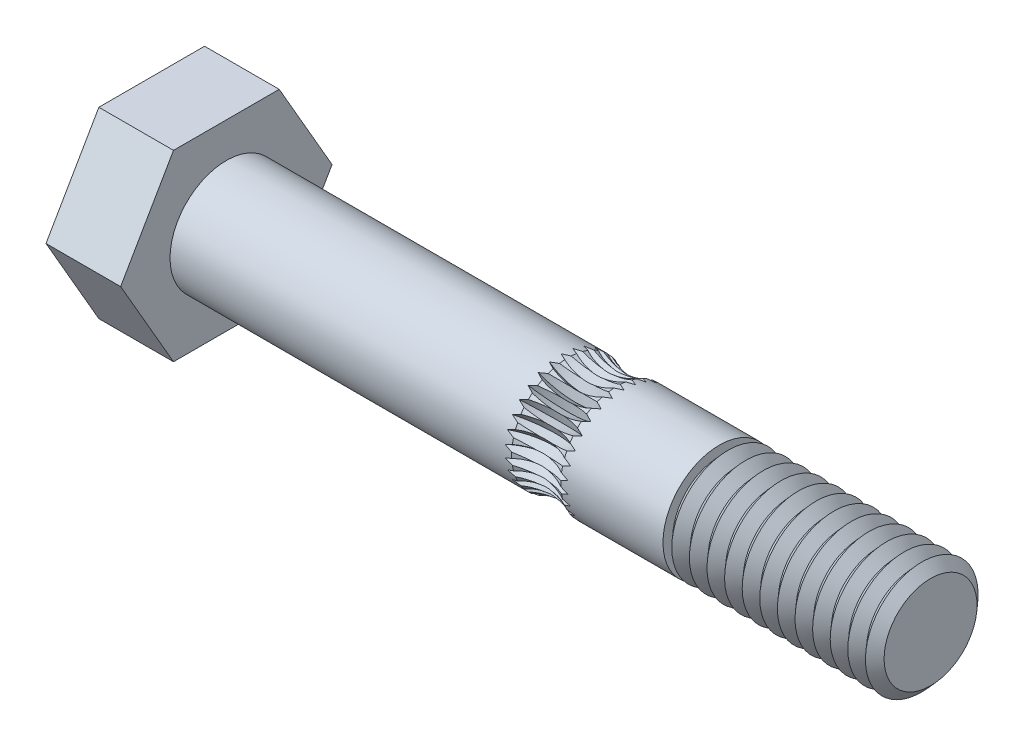
SolidWorks part; units mm, degrees
ref_plane "Front Plane" through (0, 0, 0) normal (0, 0, 1) x (1, 0, 0)
ref_plane "Top Plane" through (0, 0, 0) normal (0, 1, 0) x (1, 0, 0)
ref_plane "Right Plane" through (0, 0, 0) normal (1, 0, 0) x (0, 0, -1)
sketch "Sketch1" plane through (0, 0, 0) normal (0, 0, 1) x (1, 0, 0)
  line L0 (0, 0) -> (126.4122, 0) construction
  line L1 (0, 0) -> (0, 10)
  line L2 (0, 10) -> (5.3, 10)
  line L3 (5.3, 10) -> (5.3, 4)
  line L4 (5.3, 4) -> (29.5564, 4)
  line L5 (40.3, 4) -> (40.3, 3.3)
  line L6 (40.3, 3.3) -> (65.3, 3.3) construction
  line L7 (65.3, 3.3) -> (65.3, 0)
  line L8 (65.3, 0) -> (0, 0)
  line L9 (40.3, 4) -> (65.3, 4) construction
  line L10 (40.3, 3.3) -> (40.925, 4)
  line L11 (40.925, 4) -> (41.55, 3.3)
  line L12 (41.55, 3.3) -> (42.175, 4)
  line L13 (42.175, 4) -> (42.8, 3.3)
  line L14 (42.8, 3.3) -> (43.425, 4)
  line L15 (43.425, 4) -> (44.05, 3.3)
  line L16 (44.05, 3.3) -> (44.675, 4)
  line L17 (44.675, 4) -> (45.3, 3.3)
  line L18 (45.3, 3.3) -> (45.925, 4)
  line L19 (45.925, 4) -> (46.55, 3.3)
  line L20 (46.55, 3.3) -> (47.175, 4)
  line L21 (47.175, 4) -> (47.8, 3.3)
  line L22 (47.8, 3.3) -> (48.425, 4)
  line L23 (48.425, 4) -> (49.05, 3.3)
  line L24 (49.05, 3.3) -> (49.675, 4)
  line L25 (49.675, 4) -> (50.3, 3.3)
  line L26 (50.3, 3.3) -> (50.925, 4)
  line L27 (50.925, 4) -> (51.55, 3.3)
  line L28 (51.55, 3.3) -> (52.175, 4)
  line L29 (52.175, 4) -> (52.8, 3.3)
  line L30 (52.8, 3.3) -> (53.425, 4)
  line L31 (53.425, 4) -> (54.05, 3.3)
  line L32 (54.05, 3.3) -> (54.675, 4)
  line L33 (54.675, 4) -> (55.3, 3.3)
  line L34 (55.3, 3.3) -> (55.925, 4)
  line L35 (55.925, 4) -> (56.55, 3.3)
  line L36 (56.55, 3.3) -> (57.175, 4)
  line L37 (57.175, 4) -> (57.8, 3.3)
  line L38 (57.8, 3.3) -> (58.425, 4)
  line L39 (58.425, 4) -> (59.05, 3.3)
  line L40 (59.05, 3.3) -> (59.675, 4)
  line L41 (59.675, 4) -> (60.3, 3.3)
  line L42 (60.3, 3.3) -> (60.925, 4)
  line L43 (60.925, 4) -> (61.55, 3.3)
  line L44 (61.55, 3.3) -> (62.175, 4)
  line L45 (62.175, 4) -> (62.8, 3.3)
  line L46 (62.8, 3.3) -> (63.425, 4)
  line L47 (63.425, 4) -> (64.05, 3.3)
  line L48 (64.05, 3.3) -> (64.675, 4)
  line L49 (64.675, 4) -> (65.3, 3.3)
  line L50 (33.0436, 4) -> (40.3, 4)
  arc A0 (29.5564, 4) -> (33.0436, 4) centre (31.3, 7.6) ccw
  dimension "D10" = 3.6
  dimension "D11" = 4
  dimension "D1" = 4
  dimension "D2" = 3.3
  dimension "D3" = 25
  dimension "D4" = 60
  dimension "D5" = 5.3
  dimension "D6" = 20
  dimension "D7" = 1.25
  dimension "D8" = 0.625
  dimension "D9" = 26
revolve "Revolve1" add sketch "Sketch1" angle 360 about L0
sketch "Sketch2" plane through (0, 0, 0) normal (-1, 0, 0) x (0, 0, 1)
  line L1 (3.7528, 6.5) -> (-3.7528, 6.5)
  line L2 (-3.7528, 6.5) -> (-7.5056, 0)
  line L3 (-7.5056, 0) -> (-3.7528, -6.5)
  line L4 (-3.7528, -6.5) -> (3.7528, -6.5)
  line L5 (3.7528, -6.5) -> (7.5056, 0)
  line L6 (7.5056, 0) -> (3.7528, 6.5)
  circle A0 centre (0, 0) radius 6.5 construction
  dimension "D1" = 13
extrude "Cut-Extrude1" cut sketch "Sketch2" against normal through all flip side to cut
ref_plane "Plane1" through (31.3, 0, 0) normal (1, 0, 0) x (0, 0, -1)
sketch "Sketch3" plane through (31.3, 0, 0) normal (1, 0, 0) x (0, 0, -1)
  line L0 (-1.9187, 6) -> (2.5747, 6) construction
  line L1 (0, 0) -> (0, 6) construction
  line L2 (0, 3) -> (0.5, 3.75)
  line L3 (0.5, 3.75) -> (-0.5, 3.75)
  line L4 (-0.5, 3.75) -> (0, 3)
  dimension "D1" = 6
  dimension "D2" = 6
  dimension "D3" = 4.5
  dimension "D4" = 1
  dimension "D5" = 0.5
revolve "Cut-Revolve1" cut sketch "Sketch3" angle 360 about L0
pattern_circular "CirPattern1" count 30 over 360 about axis through (0, 0, 0) along (-1, 0, 0) of "Cut-Revolve1"
sketch "Sketch4" plane through (65.3, 0, 0) normal (1, 0, 0) x (0, 0, -1)
  circle A0 centre (0, 0) radius 8.784
extrude "Cut-Extrude2" cut sketch "Sketch4" against normal blind 10
